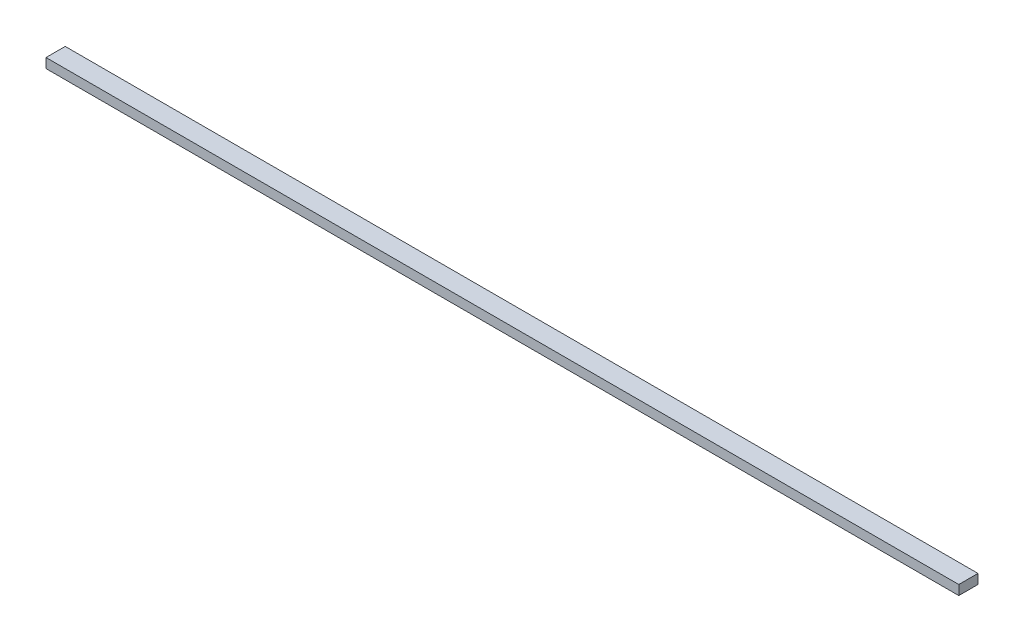
SolidWorks part; units mm, degrees
ref_plane "Plano frontal" through (0, 0, 0) normal (0, 0, 1) x (1, 0, 0)
ref_plane "Plano superior" through (0, 0, 0) normal (0, 1, 0) x (1, 0, 0)
ref_plane "Plano direito" through (0, 0, 0) normal (1, 0, 0) x (0, 0, -1)
sketch "Esboço1" plane through (0, 0, 0) normal (0, 0, 1) x (1, 0, 0)
  line L1 (0, 0) -> (4750, 0)
  line L2 (0, 0) -> (0, 50)
  line L3 (0, 50) -> (4750, 50)
  line L4 (4750, 0) -> (4750, 50)
  dimension "D1" = 4750
  dimension "D2" = 50
extrude "Ressalto-extrusão1" add sketch "Esboço1" along normal blind 100
